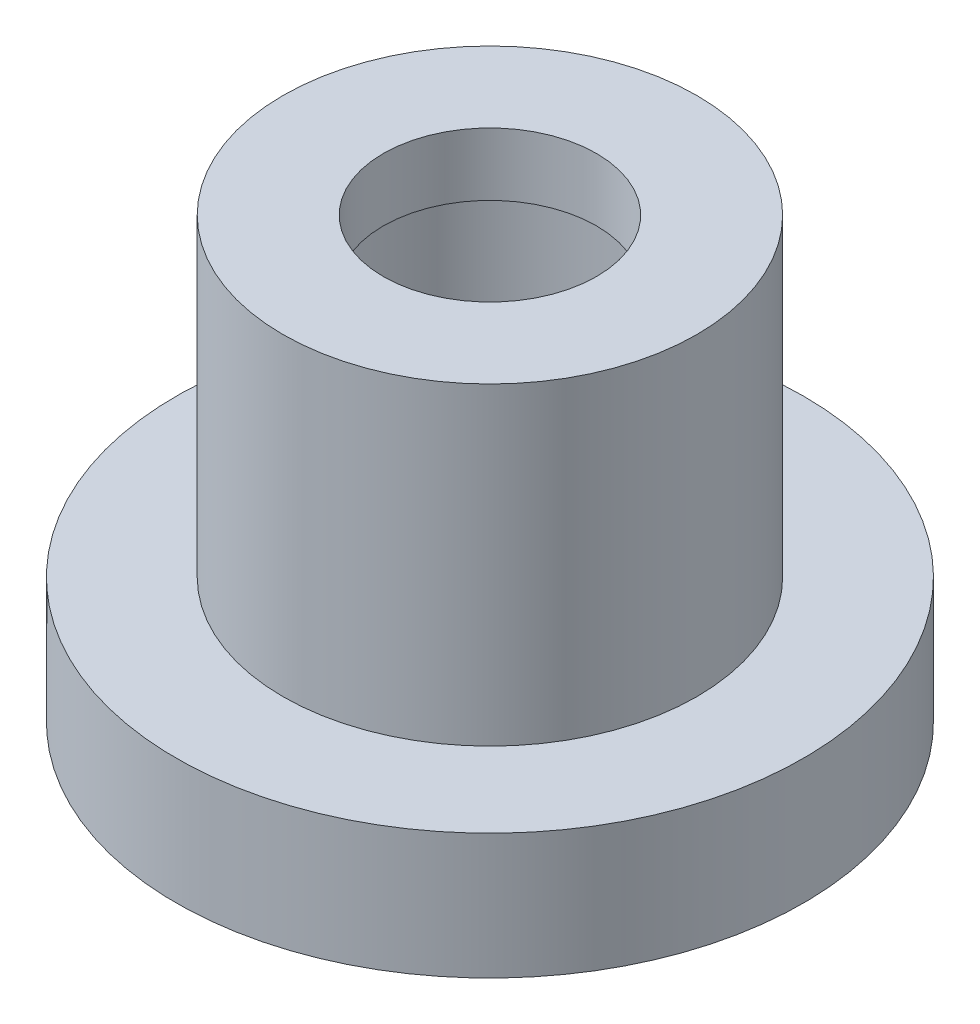
SolidWorks part; units mm, degrees
ref_plane "Front Plane" through (0, 0, 0) normal (0, 0, 1) x (1, 0, 0)
ref_plane "Top Plane" through (0, 0, 0) normal (0, 1, 0) x (1, 0, 0)
ref_plane "Right Plane" through (0, 0, 0) normal (1, 0, 0) x (0, 0, -1)
sketch "Sketch3" plane through (0, 0, 0) normal (0, 1, 0) x (1, 0, 0)
  circle A0 centre (0, 0) radius 3.3
  circle A1 centre (0, 0) radius 2.3
  dimension "D1" = 4.6
  dimension "D2" = 1
extrude "Boss-Extrude3" add sketch "Sketch3" along normal blind 7
sketch "Sketch4" plane through (0, 0, 0) normal (0, -1, 0) x (1, 0, 0)
  circle A0 centre (0, 0) radius 5
  circle A1 centre (0, 0) radius 3.3 construction
  circle A2 centre (0, 0) radius 3.3
  dimension "D1" = 10
extrude "Boss-Extrude4" add sketch "Sketch4" against normal blind 2
sketch "Sketch5" plane through (0, 7, 0) normal (0, 1, 0) x (1, 0, 0)
  circle A0 centre (0, 0) radius 2.3 construction
  circle A1 centre (0, 0) radius 2.3
  circle A2 centre (0, 0) radius 1.7
  dimension "D1" = 3.4
extrude "Boss-Extrude5" add sketch "Sketch5" against normal blind 1
